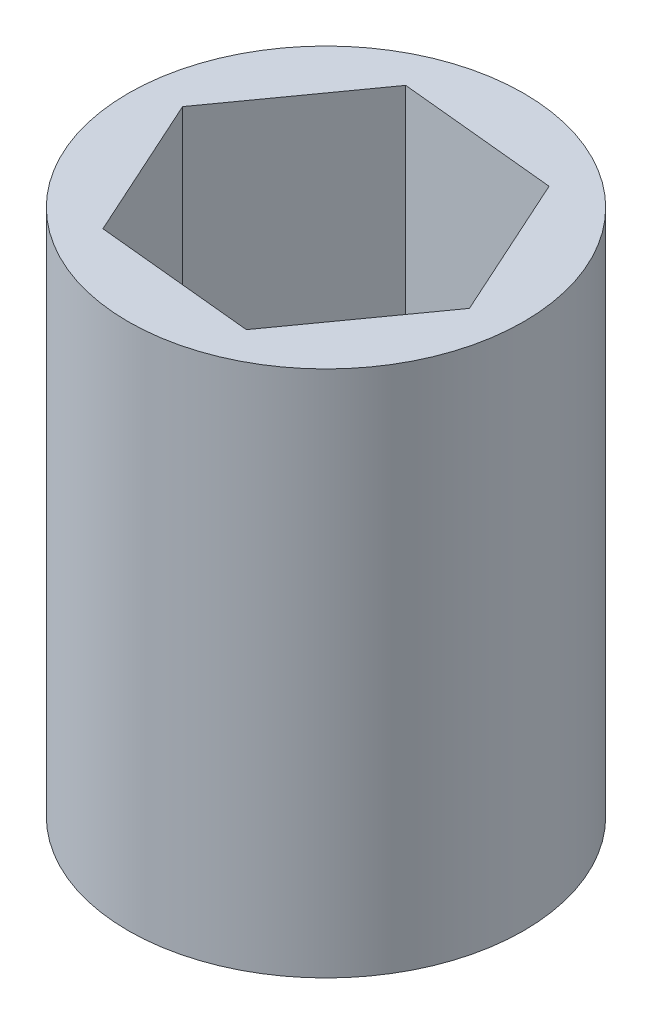
SolidWorks part; units mm, degrees
ref_plane "Front Plane" through (0, 0, 0) normal (0, 0, 1) x (1, 0, 0)
ref_plane "Top Plane" through (0, 0, 0) normal (0, 1, 0) x (1, 0, 0)
ref_plane "Right Plane" through (0, 0, 0) normal (1, 0, 0) x (0, 0, -1)
sketch "Sketch1" plane through (0, 0, 0) normal (0, 1, 0) x (1, 0, 0)
  circle A0 centre (0, 0) radius 19.05
extrude "Boss-Extrude1" add sketch "Sketch1" along normal blind 50.8
sketch "Sketch2" plane through (0, 0, 0) normal (0, -1, 0) x (1, 0, 0)
  line L1 (-15.3236, -1.5108) -> (-6.3534, -14.026)
  line L2 (-6.3534, -14.026) -> (8.9702, -12.5153)
  line L3 (8.9702, -12.5153) -> (15.3236, 1.5108)
  line L4 (15.3236, 1.5108) -> (6.3534, 14.026)
  line L5 (6.3534, 14.026) -> (-8.9702, 12.5153)
  line L6 (-8.9702, 12.5153) -> (-15.3236, -1.5108)
  circle A0 centre (0, 0) radius 13.335 construction
extrude "Cut-Extrude1" cut sketch "Sketch2" against normal up to surface (50.8 mm away) up to face at (0, 50.8, 19.05)
